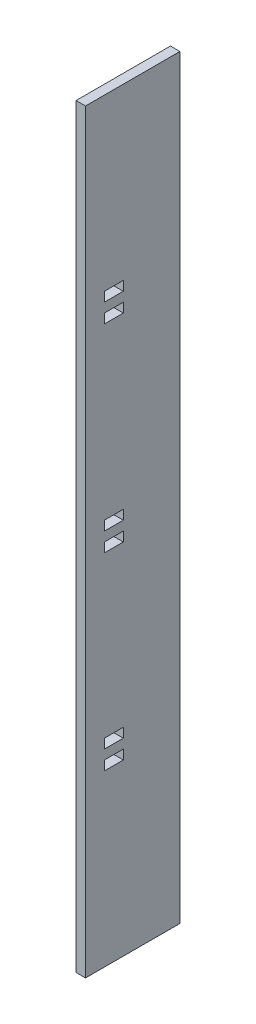
SolidWorks part; units mm, degrees
ref_plane "Front Plane" through (0, 0, 0) normal (0, 0, 1) x (1, 0, 0)
ref_plane "Top Plane" through (0, 0, 0) normal (0, 1, 0) x (1, 0, 0)
ref_plane "Right Plane" through (0, 0, 0) normal (1, 0, 0) x (0, 0, -1)
sketch "Sketch2" plane through (0, 0, 0) normal (1, 0, 0) x (0, 0, -1)
  line L0 (12.7, 254) -> (25.4, 254)
  line L1 (0, 0) -> (63.5, 0)
  line L2 (0, 0) -> (0, 508)
  line L3 (0, 508) -> (63.5, 508)
  line L4 (63.5, 0) -> (63.5, 508)
  line L5 (25.4, 387.35) -> (25.4, 393.7)
  line L6 (12.7, 260.35) -> (25.4, 260.35)
  line L7 (12.7, 260.35) -> (12.7, 254)
  line L8 (12.7, 254) -> (25.4, 254)
  line L9 (25.4, 260.35) -> (25.4, 254)
  line L10 (12.7, 127) -> (25.4, 127)
  line L11 (12.7, 127) -> (12.7, 133.35)
  line L12 (12.7, 133.35) -> (25.4, 133.35)
  line L13 (25.4, 127) -> (25.4, 133.35)
  line L14 (12.7, 120.65) -> (25.4, 120.65)
  line L15 (12.7, 120.65) -> (12.7, 114.3)
  line L16 (12.7, 114.3) -> (25.4, 114.3)
  line L17 (25.4, 120.65) -> (25.4, 114.3)
  line L18 (12.7, 247.65) -> (25.4, 247.65)
  line L19 (12.7, 247.65) -> (12.7, 241.3)
  line L20 (12.7, 241.3) -> (25.4, 241.3)
  line L21 (25.4, 247.65) -> (25.4, 241.3)
  line L22 (12.7, 393.7) -> (25.4, 393.7)
  line L23 (12.7, 387.35) -> (12.7, 393.7)
  line L24 (12.7, 387.35) -> (25.4, 387.35)
  line L25 (25.4, 381) -> (25.4, 374.65)
  line L26 (12.7, 374.65) -> (25.4, 374.65)
  line L27 (12.7, 381) -> (12.7, 374.65)
  line L28 (12.7, 381) -> (25.4, 381)
  dimension "D1" = 63.5
  dimension "D2" = 508
  dimension "D3" = 127
  dimension "D4" = 6.35
  dimension "D5" = 6.35
  dimension "D6" = 6.35
  dimension "D7" = 12.7
  dimension "D8" = 12.7
  dimension "D9" = 12.7
  dimension "D10" = 12.7
  dimension "D11" = 12.7
  dimension "D12" = 12.7
  dimension "D13" = 6.35
  dimension "D14" = 6.35
  dimension "D15" = 6.35
  dimension "D16" = 12.7
extrude "Boss-Extrude1" add sketch "Sketch2" along normal blind 6.35 contours L1 L4 L3 L2 L24 L23 L22 L5 L13 L10 L11 L12 L6 L9 L0 L7 L14 L17 L16 L15 L18 L21 L20 L19 L27 L28 L25 L26
